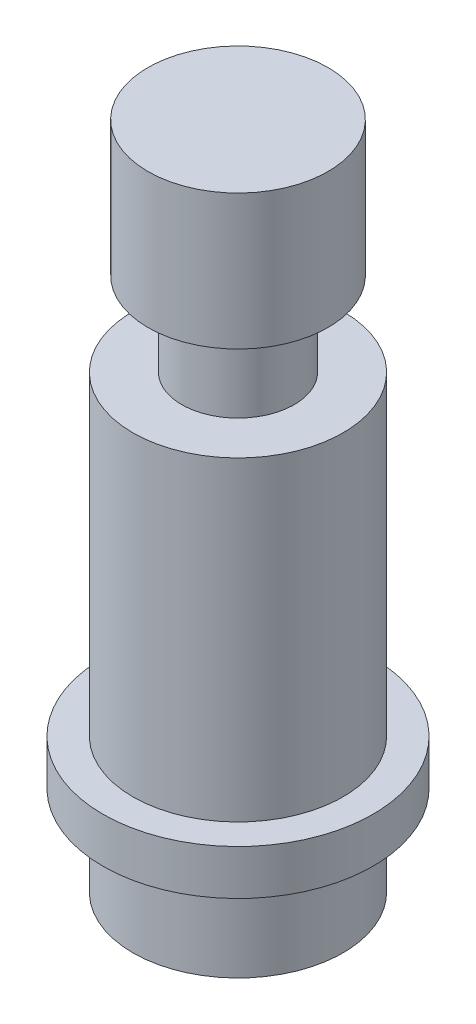
SolidWorks part; units mm, degrees
material "1023 Carbon Steel Sheet (SS)"
ref_plane "Front" through (0, 0, 0) normal (0, 0, 1) x (1, 0, 0)
ref_plane "Top" through (0, 0, 0) normal (0, 1, 0) x (1, 0, 0)
ref_plane "Right" through (0, 0, 0) normal (1, 0, 0) x (0, 0, -1)
sketch "Sketch1" plane through (0, 0, 0) normal (1, 0, 0) x (0, 0, -1)
  line L0 (0, 0) -> (0, 59.589) construction
  line L1 (0, 0) -> (-7, 0)
  line L2 (-7, 0) -> (-7, 6)
  line L3 (-7, 6) -> (-9, 6)
  line L4 (-9, 6) -> (-9, 9)
  line L5 (-9, 9) -> (-7, 9)
  line L6 (-7, 9) -> (-7, 30)
  line L7 (-7, 30) -> (-3.75, 30)
  line L8 (-3.75, 30) -> (-3.75, 35.5739)
  line L9 (-3.75, 35.5739) -> (-6, 35.5739)
  line L10 (-6, 35.5739) -> (-6, 44.5739)
  line L11 (-6, 44.5739) -> (0, 44.5739)
  line L12 (0, 0) -> (0, 44.5739)
  dimension "D1" = 6
  dimension "D2" = 21
  dimension "D3" = 9
  dimension "D6" = 14
  dimension "D7" = 18
  dimension "D8" = 7.5
  dimension "D9" = 12
revolve "Revolve1" add sketch "Sketch1" angle 360 about L0
